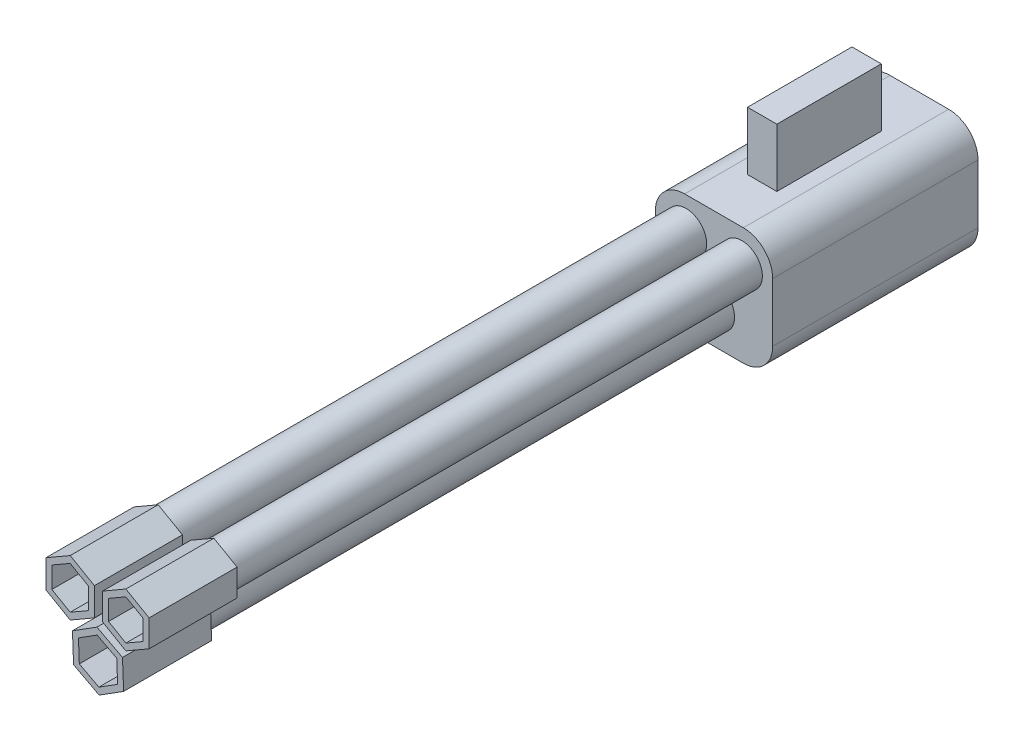
SolidWorks part; units mm, degrees
ref_plane "Ön Düzlem" through (0, 0, 0) normal (0, 0, 1) x (1, 0, 0)
ref_plane "Üst Düzlem" through (0, 0, 0) normal (0, 1, 0) x (1, 0, 0)
ref_plane "Sağ Düzlem" through (0, 0, 0) normal (1, 0, 0) x (0, 0, -1)
sketch "Çizim1" plane through (0, 0, 0) normal (0, 0, 1) x (1, 0, 0)
  line L1 (-2, 1.647) -> (2, 1.647)
  line L2 (-2, 1.647) -> (-2, -2.353)
  line L3 (-2, -2.353) -> (2, -2.353)
  line L4 (2, 1.647) -> (2, -2.353)
  point P0 (0, 0)
  dimension "D1" = 4
  dimension "D2" = 4
extrude "Yükseklik-Ekstrüzyon1" add sketch "Çizim1" along normal blind 7 contours L4 L3 L2 L1
fillet "Radyus1" radius 1 1 edges at (2, -2.353, 3.5)
fillet "Radyus2" radius 1 1 edges at (-2, 1.647, 3.5)
fillet "Radyus3" radius 1 1 edges at (2, 1.647, 3.5)
fillet "Radyus4" radius 1 1 edges at (-2, -2.353, 3.5)
sketch "Çizim3" plane through (0, 0, 7) normal (0, 0, 1) x (1, 0, 0)
  circle A0 centre (-0.9492, 0.5425) radius 0.5
  circle A1 centre (0.9492, 0.5425) radius 0.5
  circle A2 centre (0, -1.147) radius 0.5
  dimension "D1" = 1
  dimension "D2" = 1
  dimension "D3" = 1
extrude "Ekstrüzyon-İnce1" add sketch "Çizim3" along normal blind 18 thin
ref_plane "Düzlem1" through (0, 0, 25) normal (0, 0, 1) x (1, 0, 0)
sketch "Çizim4" plane through (0, 0, 25) normal (0, 0, 1) x (1, 0, 0)
  line L1 (-0.9492, -0.4099) -> (-0.1244, 0.0663)
  line L2 (-0.1244, 0.0663) -> (-0.1244, 1.0187)
  line L3 (-0.1244, 1.0187) -> (-0.9492, 1.4948)
  line L4 (-0.9492, 1.4948) -> (-1.774, 1.0187)
  line L5 (-1.774, 1.0187) -> (-1.774, 0.0663)
  line L6 (-1.774, 0.0663) -> (-0.9492, -0.4099)
  line L7 (0.9492, -0.3712) -> (1.7404, 0.0857)
  line L8 (1.7404, 0.0857) -> (1.7404, 0.9993)
  line L9 (1.7404, 0.9993) -> (0.9492, 1.4561)
  line L10 (0.9492, 1.4561) -> (0.158, 0.9993)
  line L11 (0.158, 0.9993) -> (0.158, 0.0857)
  line L12 (0.158, 0.0857) -> (0.9492, -0.3712)
  line L13 (0.8716, -1.6067) -> (0.8339, -0.622)
  line L14 (0.8339, -0.622) -> (-0.0377, -0.1623)
  line L15 (-0.0377, -0.1623) -> (-0.8716, -0.6873)
  line L16 (-0.8716, -0.6873) -> (-0.8339, -1.672)
  line L17 (-0.8339, -1.672) -> (0.0377, -2.1317)
  line L18 (0.0377, -2.1317) -> (0.8716, -1.6067)
  circle A0 centre (-0.9492, 0.5425) radius 0.8248 construction
  circle A1 centre (0.9492, 0.5425) radius 0.7912 construction
  circle A2 centre (0, -1.147) radius 0.8534 construction
sketch "Çizim6" plane through (0, 0, 0) normal (1, 0, 0) x (0, 0, -1)
  line L0 (0, 1.647) -> (-7, 1.647) construction
  line L1 (-1.7961, 1.647) -> (-5.3577, 1.647)
  line L2 (-1.7961, 1.647) -> (-1.7961, 3.635)
  line L3 (-1.7961, 3.635) -> (-5.3577, 3.635)
  line L4 (-5.3577, 1.647) -> (-5.3577, 3.635)
extrude "Yükseklik-Ekstrüzyon2" add sketch "Çizim6" along normal blind 0.5 and the other way blind 0.5
extrude "Ekstrüzyon-İnce3" add sketch "Çizim4" along normal blind 3 thin thin type one direction reverse wall 0.2
